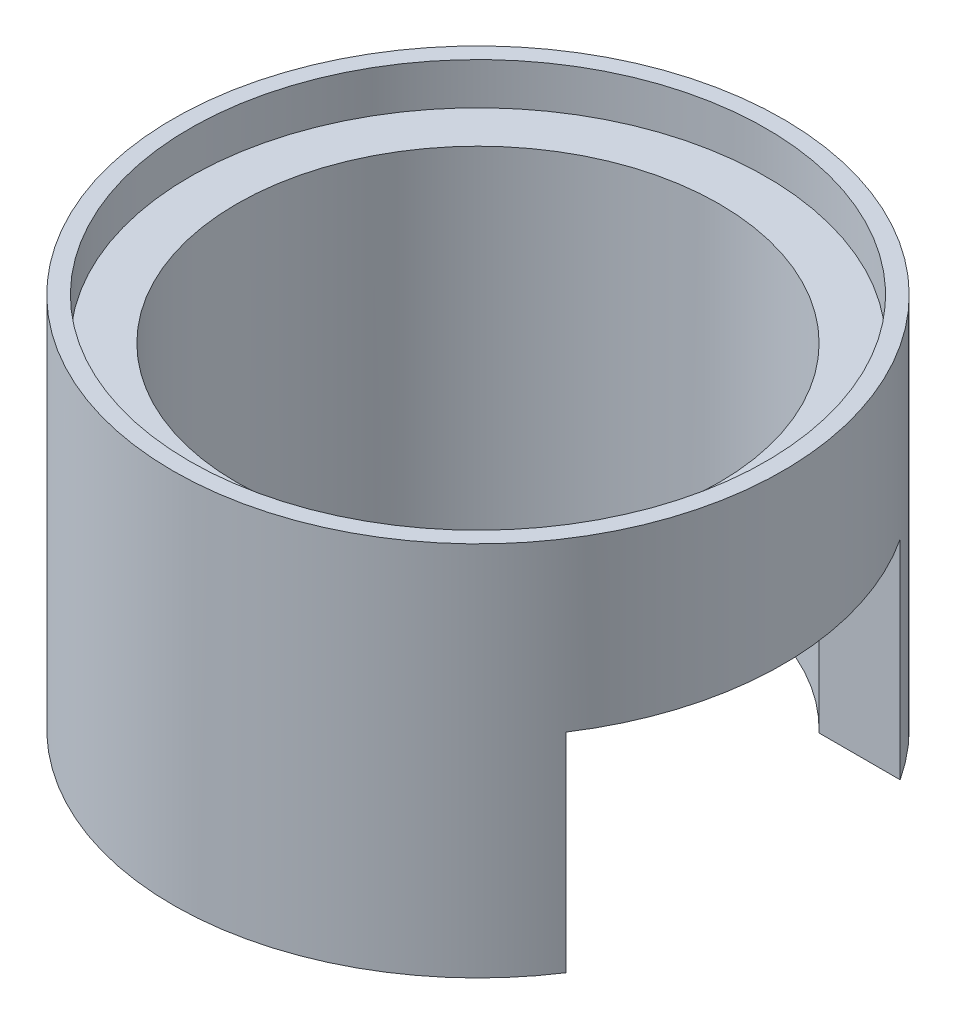
SolidWorks part; units mm, degrees
ref_plane "Front Plane" through (0, 0, 0) normal (0, 0, 1) x (1, 0, 0)
ref_plane "Top Plane" through (0, 0, 0) normal (0, 1, 0) x (1, 0, 0)
ref_plane "Right Plane" through (0, 0, 0) normal (1, 0, 0) x (0, 0, -1)
sketch "Sketch1" plane through (0, 0, 0) normal (0, 1, 0) x (1, 0, 0)
  circle A0 centre (0, 0) radius 7.3
  dimension "D1" = 14.6
extrude "Boss-Extrude1" add sketch "Sketch1" along normal blind 9
sketch "Sketch2" plane through (0, 9, 0) normal (0, 1, 0) x (1, 0, 0)
  circle A0 centre (0, 0) radius 6.9
  dimension "D1" = 13.8
extrude "Cut-Extrude1" cut sketch "Sketch2" against normal blind 1
sketch "Sketch3" plane through (0, 0, 0) normal (0, -1, 0) x (1, 0, 0)
  circle A0 centre (0, 0) radius 5
  dimension "D1" = 10
extrude "Cut-Extrude2" cut sketch "Sketch3" against normal blind 7
sketch "Sketch4" plane through (0, 8, 0) normal (0, 1, 0) x (1, 0, 0)
  circle A0 centre (0, 0) radius 5.775
  dimension "D1" = 11.55
extrude "Cut-Extrude3" cut sketch "Sketch4" against normal through all
ref_plane "Plane1" through (7.3, 0, 0) normal (1, 0, 0) x (0, 0, -1)
sketch "Sketch5" plane through (7.3, 0, 0) normal (1, 0, 0) x (0, 0, -1)
  line L0 (0, 0) -> (0, 9)
  line L1 (7.3, 9) -> (-7.3, 9) construction
  line L2 (-4, 0) -> (4, 0)
  line L3 (8.03, 0) -> (-8.03, 0) construction
  line L4 (-4, 0) -> (-4, 4.9892)
  line L5 (-4, 4.9892) -> (4, 4.9892)
  line L6 (4, 4.9892) -> (4, 0)
  point P9 (0, 0)
  dimension "D1" = 8
  dimension "D2" = 8
extrude "Cut-Extrude4" cut sketch "Sketch5" against normal blind 6 contours L5 L4 L2 L0 | L6 L5 L0 L2
